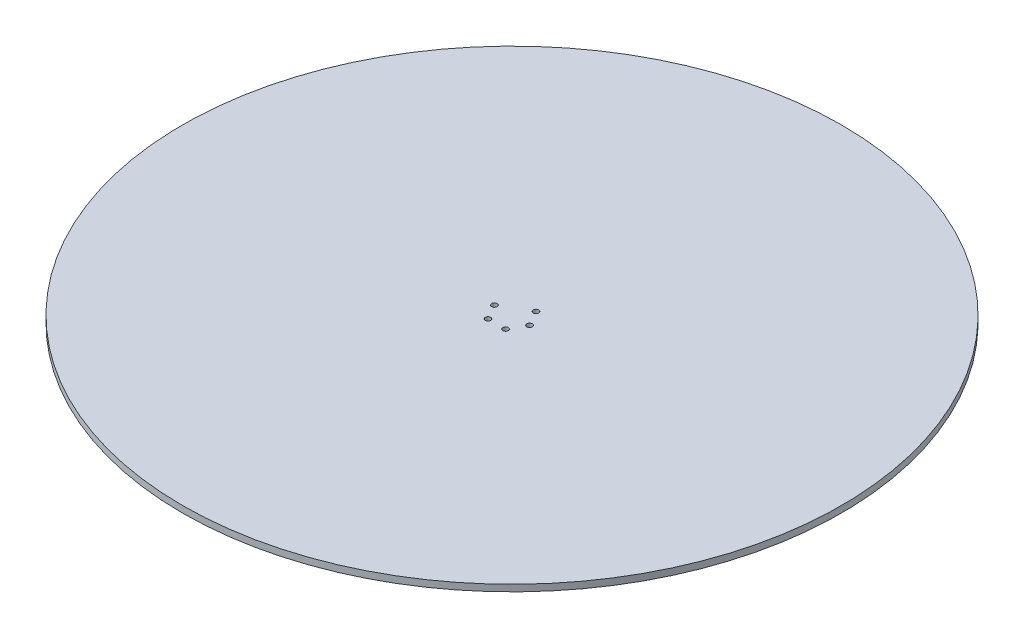
SolidWorks part; units mm, degrees
ref_plane "Front Plane" through (0, 0, 0) normal (0, 0, 1) x (1, 0, 0)
ref_plane "Top Plane" through (0, 0, 0) normal (0, 1, 0) x (1, 0, 0)
ref_plane "Right Plane" through (0, 0, 0) normal (1, 0, 0) x (0, 0, -1)
sketch "Sketch1" plane through (0, 0, 0) normal (0, 1, 0) x (1, 0, 0)
  circle A0 centre (0, 0) radius 150
  dimension "D1" = 300
extrude "Boss-Extrude1" add sketch "Sketch1" along normal blind 3
sketch "Sketch3" plane through (0, 0, 0) normal (0, -1, 0) x (1, 0, 0)
  circle A0 centre (8, 0) radius 1.25 construction
  circle A1 centre (4, 6.9282) radius 1.25 construction
  circle A2 centre (4, -6.9282) radius 1.25 construction
  circle A3 centre (-4, 6.9282) radius 1.25 construction
  circle A4 centre (-8, 0) radius 1.25 construction
  circle A5 centre (8, 0) radius 1.25
  circle A6 centre (4, 6.9282) radius 1.25
  circle A7 centre (4, -6.9282) radius 1.25
  circle A8 centre (-4, 6.9282) radius 1.25
  circle A9 centre (-8, 0) radius 1.25
extrude "Cut-Extrude1" cut sketch "Sketch3" against normal blind 10
